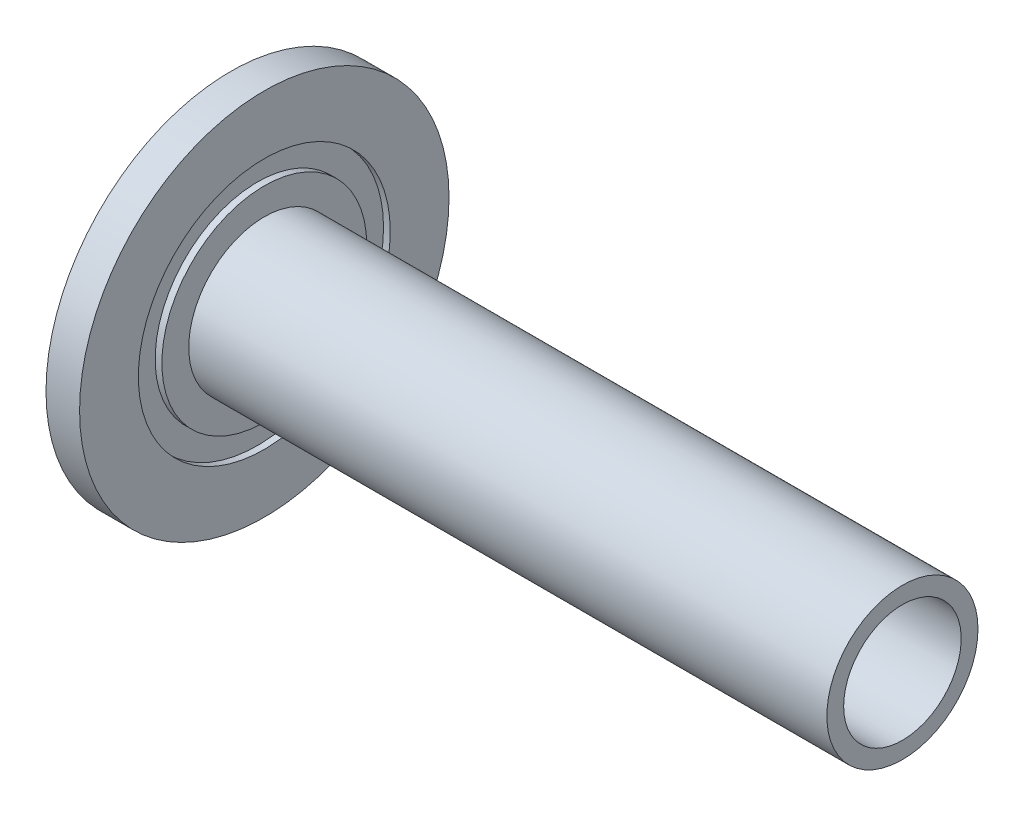
SolidWorks part; units mm, degrees
ref_plane "Front Plane" through (0, 0, 0) normal (0, 0, 1) x (1, 0, 0)
ref_plane "Top Plane" through (0, 0, 0) normal (0, 1, 0) x (1, 0, 0)
ref_plane "Right Plane" through (0, 0, 0) normal (1, 0, 0) x (0, 0, -1)
sketch "Sketch2" plane through (0, 0, 0) normal (1, 0, 0) x (0, 0, -1)
  circle A0 centre (0, 0) radius 55
extrude "Boss-Extrude1" add sketch "Sketch2" along normal blind 10
sketch "Sketch3" plane through (10, 0, 0) normal (1, 0, 0) x (0, 0, -1)
  circle A0 centre (0, 0) radius 22.5
extrude "Boss-Extrude2" add sketch "Sketch3" along normal blind 190
sketch "Sketch4" plane through (0, 0, 0) normal (-1, 0, 0) x (0, 0, 1)
  circle A0 centre (0, 0) radius 17.5
extrude "Cut-Extrude1" cut sketch "Sketch4" against normal through all both and the other way through all
sketch "Sketch14" plane through (0, 0, 0) normal (-1, 0, 0) x (0, 0, 1)
  circle A0 centre (0, 0) radius 30.5
  circle A1 centre (0, 0) radius 37.5
sketch "Sketch15" plane through (10, 0, 0) normal (1, 0, 0) x (0, 0, -1)
  circle A0 centre (0, 0) radius 30.5
  circle A1 centre (0, 0) radius 37.5
extrude "Cut-Extrude5" cut sketch "Sketch14" against normal blind 1
extrude "Cut-Extrude6" cut sketch "Sketch15" against normal blind 2
sketch "Sketch16" plane through (0, 0, 0) normal (-1, 0, 0) x (0, 0, 1)
  circle A0 centre (0, 34) radius 2.5
  circle A1 centre (0, -34) radius 2.5
extrude "Cut-Extrude7" cut sketch "Sketch16" against normal blind 4
sketch "Sketch17" plane through (0, 0, 0) normal (-1, 0, 0) x (0, 0, 1)
  circle A0 centre (0, -34) radius 5
  circle A1 centre (0, 34) radius 5
extrude "Cut-Extrude8" cut sketch "Sketch17" against normal blind 2
